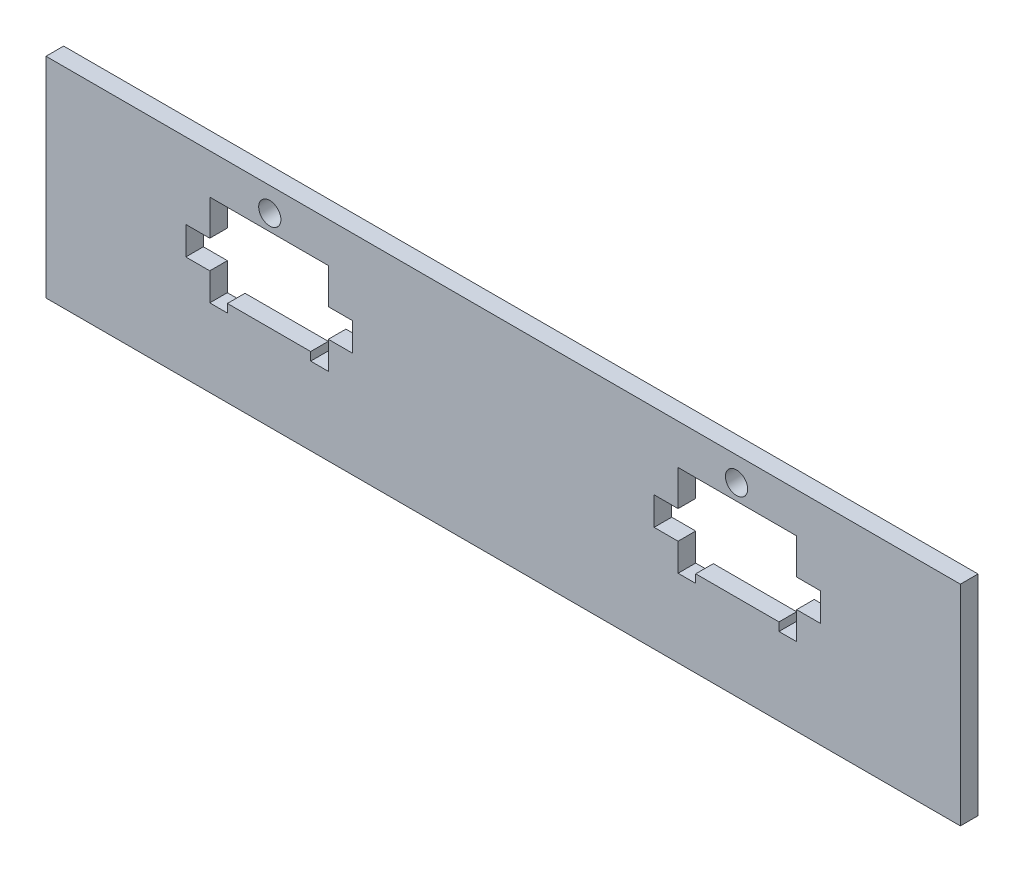
SolidWorks part; units mm, degrees
ref_plane "Front Plane" through (0, 0, 0) normal (0, 0, 1) x (1, 0, 0)
ref_plane "Top Plane" through (0, 0, 0) normal (0, 1, 0) x (1, 0, 0)
ref_plane "Right Plane" through (0, 0, 0) normal (1, 0, 0) x (0, 0, -1)
sketch "Sketch1" plane through (0, 0, 0) normal (0, 0, 1) x (1, 0, 0)
  line L0 (-30.5652, -17.1761) -> (-30.5652, -28.8321) construction
  line L5 (-27.3902, -18.9121) -> (-12.3902, -18.9121)
  line L7 (-27.3902, -18.9121) -> (-27.3902, -33.9121)
  line L13 (-12.3902, -18.9121) -> (-12.3902, -33.9121)
  line L17 (-38.0632, -14.8639) -> (-1.7172, -14.8639)
  line L22 (-38.0632, -14.8639) -> (-38.0632, -33.9121)
  line L31 (-35.1182, -17.1761) -> (-4.8922, -17.1761) construction
  line L35 (-1.7172, -14.8639) -> (-1.7172, -33.9121)
  line L36 (-9.2102, -17.1761) -> (-9.2102, -28.8321) construction
  line L48 (-38.0632, -33.9121) -> (-27.3902, -33.9121)
  line L49 (-12.3902, -33.9121) -> (-1.7172, -33.9121)
  dimension "D1" = 15
  dimension "D2" = 15
  dimension "D3" = 3.175
  dimension "D8" = 30.226
extrude "Boss-Extrude1" add sketch "Sketch1" against normal blind 3.175
sketch "Sketch8" plane through (0, 0, 0) normal (0, 0, 1) x (1, 0, 0)
  line L0 (-38.0632, -33.9121) -> (-1.7172, -33.9121) construction
  line L1 (-38.0632, -14.8639) -> (-1.7172, -14.8639) construction
  line L2 (-1.7172, -37.0871) -> (-1.7172, -33.9121)
  line L4 (-38.0632, -33.9121) -> (-38.0632, -37.0871)
  line L5 (-38.0632, -37.0871) -> (-1.7172, -37.0871)
  line L7 (-38.0632, -14.8639) -> (-1.7172, -14.8639)
  line L8 (-38.0632, -14.8639) -> (-38.0632, -11.6889)
  line L9 (-38.0632, -11.6889) -> (-1.7172, -11.6889)
  line L10 (-1.7172, -14.8639) -> (-1.7172, -11.6889)
  line L11 (-1.7172, -33.9121) -> (-38.0632, -33.9121)
  dimension "D1" = 3.175
  dimension "D2" = 3.175
extrude "Boss-Extrude3" add sketch "Sketch8" against normal up to surface (3.175 mm away) up to face at (-19.8902, -25.4001, -3.175)
sketch "Sketch7" plane through (0, 0, 0) normal (0, 0, 1) x (1, 0, 0)
  line L0 (-19.7528, -18.9121) -> (-19.7528, -27.4799) construction
  circle A2 centre (-19.7528, -16.0271) radius 2
extrude "LED hole" cut sketch "Sketch7" against normal through all
sketch "Sketch2" plane through (0, 0, 0) normal (0, 0, 1) x (1, 0, 0)
  line L0 (-38.0632, -37.0871) -> (-1.7172, -37.0871) construction
  line L5 (-34.8882, -33.9121) -> (-4.8922, -33.9121)
  line L6 (-4.8922, -33.9121) -> (-4.8922, -18.9121)
  line L7 (-34.8882, -33.9121) -> (-34.8882, -18.9121)
  line L8 (-4.8922, -18.9121) -> (-34.8882, -18.9121)
  line L9 (-38.0632, -11.6889) -> (-38.0632, -37.0871) construction
  dimension "D1" = 3.175
  dimension "D2" = 15
  dimension "D3" = 3.175
extrude "Cut-Extrude1" [suppressed] cut sketch "Sketch2" against normal blind 10
sketch "Sketch3" [suppressed] plane through (0, 0, 0) normal (0, 0, 1) x (1, 0, 0)
  line L0 (-34.8882, -18.9121) -> (-34.8882, -33.9121) construction
  line L1 (-27.3882, -18.9121) -> (-12.3882, -18.9121)
  line L2 (-27.3882, -18.9121) -> (-27.3882, -33.9121)
  line L3 (-27.3882, -33.9121) -> (-12.3882, -33.9121)
  line L4 (-12.3882, -18.9121) -> (-12.3882, -33.9121)
  dimension "D1" = 15
  dimension "D2" = 15
  dimension "D3" = 7.5
extrude "Boss-Extrude2" [suppressed] add sketch "Sketch3" against normal blind 3.175
sketch "Sketch9" [suppressed] plane through (0, 0, 0) normal (0, 0, 1) x (1, 0, 0)
  line L0 (-27.3882, -18.9121) -> (-12.3882, -18.9121) construction
  line L1 (-17.7528, -16.0271) -> (-17.7528, -18.9121)
  line L2 (-21.7528, -16.0271) -> (-21.7528, -18.9121)
  line L3 (-21.7528, -18.9121) -> (-21.7528, -19.4514)
  line L4 (-21.2528, -19.9514) -> (-18.2528, -19.9514)
  line L5 (-17.7528, -19.4514) -> (-17.7528, -18.9121)
  circle A0 centre (-19.7528, -16.0271) radius 2 construction
  circle A1 centre (-19.7528, -16.0271) radius 2 construction
  arc A2 (-21.7528, -16.0271) -> (-17.7528, -16.0271) centre (-19.7528, -16.0271) ccw
  arc A3 (-18.2528, -19.9514) -> (-17.7528, -19.4514) centre (-18.2528, -19.4514) ccw
  arc A4 (-21.2528, -19.9514) -> (-21.7528, -19.4514) centre (-21.2528, -19.4514) cw
  dimension "D1" = 0.5
extrude "Cut-Extrude2" [suppressed] cut sketch "Sketch9" against normal through all
sketch "Sketch10" plane through (0, 0, 0) normal (0, 0, 1) x (1, 0, 0)
  line L2 (-38.0632, -37.0871) -> (-1.7172, -37.0871)
  line L3 (-38.0632, -37.0871) -> (-38.0632, -49.4061)
  line L4 (-38.0632, -49.4061) -> (-1.7172, -49.4061)
  line L5 (-1.7172, -37.0871) -> (-1.7172, -49.4061)
  dimension "D2" = 12.319
extrude "Lower part" add sketch "Sketch10" against normal up to surface (3.175 mm away) up to face at (-17.7528, -16.0271, -3.175)
sketch "Sketch13" [suppressed] plane through (0, 0, -3.175) normal (0, 0, -1) x (-1, 0, 0)
  line L1 (4.8922, -18.9121) -> (12.3882, -18.9121)
  line L2 (4.8922, -18.9121) -> (4.8922, -33.9121)
  line L3 (4.8922, -33.9121) -> (12.3882, -33.9121)
  line L4 (12.3882, -18.9121) -> (12.3882, -33.9121)
  line L5 (27.3882, -18.9121) -> (34.8882, -18.9121)
  line L6 (27.3882, -18.9121) -> (27.3882, -33.9121)
  line L7 (27.3882, -33.9121) -> (34.8882, -33.9121)
  line L8 (34.8882, -18.9121) -> (34.8882, -33.9121)
extrude "Boss-Extrude4" [suppressed] add sketch "Sketch13" against normal blind 3.175
sketch "Sketch12" plane through (0, 0, -3.175) normal (0, 0, -1) x (-1, 0, 0)
  line L2 (12.3902, -33.9121) -> (12.3902, -18.9121)
  line L4 (9.2152, -30.7371) -> (9.2152, -22.0921)
  line L6 (27.3902, -18.9121) -> (27.3902, -33.9121)
  line L8 (30.5652, -22.0871) -> (30.5652, -30.7321)
  line L21 (9.2152, -18.9121) -> (12.3902, -18.9121)
  line L26 (9.2152, -33.9121) -> (12.3902, -33.9121)
  line L27 (27.3902, -18.9121) -> (30.5652, -18.9121)
  line L28 (27.3902, -33.9121) -> (30.5652, -33.9121)
  line L29 (30.5652, -22.0871) -> (30.5652, -18.9121)
  line L30 (9.2152, -22.0921) -> (9.2152, -18.9121)
  line L31 (9.2152, -30.7371) -> (9.2152, -33.9121)
  line L32 (30.5652, -30.7321) -> (30.5652, -33.9121)
  dimension "D1" = 3.175
  dimension "D2" = 3.175
extrude "Cut-Extrude3" cut sketch "Sketch12" against normal through all
sketch "Sketch11" plane through (0, 0, 0) normal (0, 0, 1) x (1, 0, 0)
  line L2 (-34.8852, -25.3321) -> (-34.8852, -30.4121)
  line L5 (-9.2153, -25.3321) -> (-4.9003, -25.3321)
  line L7 (-9.2153, -30.4121) -> (-4.9003, -30.4121)
  line L8 (-4.9003, -25.3321) -> (-4.9003, -30.4121)
  line L11 (-34.8852, -25.3321) -> (-30.5652, -25.3321)
  line L13 (-9.2153, -25.3321) -> (-9.2153, -30.4121)
  line L14 (-30.5652, -33.9121) -> (-30.5652, -18.9121) construction
  line L15 (-30.5652, -25.3321) -> (-30.5652, -30.4121)
  line L17 (-30.5652, -30.4121) -> (-34.8852, -30.4121)
  dimension "D2" = 5.08
  dimension "D4" = 5.08
  dimension "D6" = 4.315
extrude "IR Hole" cut sketch "Sketch11" against normal through all
sketch "Sketch14" plane through (0, 0, -3.175) normal (0, 0, -1) x (-1, 0, 0)
  line L0 (1.7172, -49.4061) -> (38.0632, -49.4061) construction
  line L1 (1.7172, -11.6889) -> (-22.2858, -11.6889)
  line L2 (1.7172, -11.6889) -> (1.7172, -49.4061)
  line L3 (1.7172, -49.4061) -> (-22.2858, -49.4061)
  line L4 (-22.2858, -11.6889) -> (-22.2858, -49.4061)
  line L6 (38.0632, -11.6889) -> (60.0632, -11.6889)
  line L7 (38.0632, -11.6889) -> (38.0632, -49.4061)
  line L8 (38.0632, -49.4061) -> (60.0632, -49.4061)
  line L9 (60.0632, -11.6889) -> (60.0632, -49.4061)
  dimension "D1" = 24.003
  dimension "D2" = 0
  dimension "D3" = 22
extrude "Boss-Extrude5" add sketch "Sketch14" against normal blind 3.175
sketch "Sketch19" plane through (0, 0, 0) normal (0, 0, 1) x (1, 0, 0)
  line L1 (-30.5652, -33.9121) -> (-27.3902, -33.9121)
  line L2 (-30.5652, -33.9121) -> (-30.5652, -35.4121)
  line L3 (-30.5652, -35.4121) -> (-27.3902, -35.4121)
  line L4 (-27.3902, -33.9121) -> (-27.3902, -35.4121)
  line L5 (-12.3902, -33.9121) -> (-9.2152, -33.9121)
  line L6 (-12.3902, -33.9121) -> (-12.3902, -35.4121)
  line L7 (-12.3902, -35.4121) -> (-9.2152, -35.4121)
  line L8 (-9.2152, -33.9121) -> (-9.2152, -35.4121)
  dimension "D1" = 1.5
  dimension "D2" = 1.5
  dimension "D3" = 3.175
  dimension "D4" = 3.175
extrude "bottom groove for side part" cut sketch "Sketch19" against normal up to surface (3.175 mm away) up to face at (-19.8911, -27.3855, -3.175)
sketch "Sketch17" [suppressed] plane through (0, 0, -3.175) normal (0, 0, -1) x (-1, 0, 0)
  line L1 (27.3902, -18.9121) -> (30.5652, -18.9121)
  line L2 (27.3902, -18.9121) -> (27.3902, -33.919)
  line L3 (27.3902, -33.919) -> (30.5652, -33.919)
  line L4 (30.5652, -18.9121) -> (30.5652, -33.919)
  line L5 (12.3902, -18.9121) -> (9.2152, -18.9121)
  line L6 (12.3902, -18.9121) -> (12.3902, -33.919)
  line L7 (12.3902, -33.919) -> (9.2152, -33.919)
  line L8 (9.2152, -18.9121) -> (9.2152, -33.919)
extrude "Cut-Extrude6" [suppressed] cut sketch "Sketch17" against normal blind 10
ref_plane "Plane1" through (22.2858, 0, 0) normal (1, 0, 0) x (0, 0, -1)
mirror "Mirror9 - front face" [suppressed] about plane through (22.2858, 0, 0) normal (1, 0, 0)
mirror "Mirror10 - back face" [suppressed] about plane through (22.2858, 0, 0) normal (1, 0, 0)
mirror "Mirror1" about plane through (22.2858, 0, 0) normal (1, 0, 0) of bodies 126 117
sketch "Sketch15" [suppressed] plane through (0, 0, -3.175) normal (0, 0, -1) x (-1, 0, 0)
  line L0 (-104.6348, -21.6889) -> (60.0632, -21.6889) construction
  line L1 (-104.6348, -49.4061) -> (-104.6348, -11.6889) construction
  line L2 (60.0632, -49.4061) -> (60.0632, -11.6889) construction
  line L4 (60.0632, -11.6889) -> (-104.6348, -11.6889) construction
  line L5 (-104.6348, -39.4061) -> (60.0632, -39.4061) construction
  line L6 (-104.6348, -49.4061) -> (60.0632, -49.4061) construction
  line L7 (-89.6348, -11.6889) -> (-89.6348, -49.4061) construction
  line L8 (45.0632, -11.6889) -> (45.0632, -49.4061) construction
  line L9 (-22.2858, 1.7462) -> (-22.2858, -1.7463) construction
  circle A0 centre (-89.6348, -21.6889) radius 5
  circle A1 centre (-89.6348, -39.4061) radius 5
  circle A2 centre (-22.2858, -21.6889) radius 5
  circle A3 centre (-22.2858, -39.4061) radius 5
  circle A4 centre (45.0632, -21.6889) radius 5
  circle A5 centre (45.0632, -39.4061) radius 5
  dimension "D1" = 10
  dimension "D2" = 10
  dimension "D3" = 15
  dimension "D4" = 15
extrude "Cut-Extrude4" [suppressed] cut sketch "Sketch15" against normal blind 10
